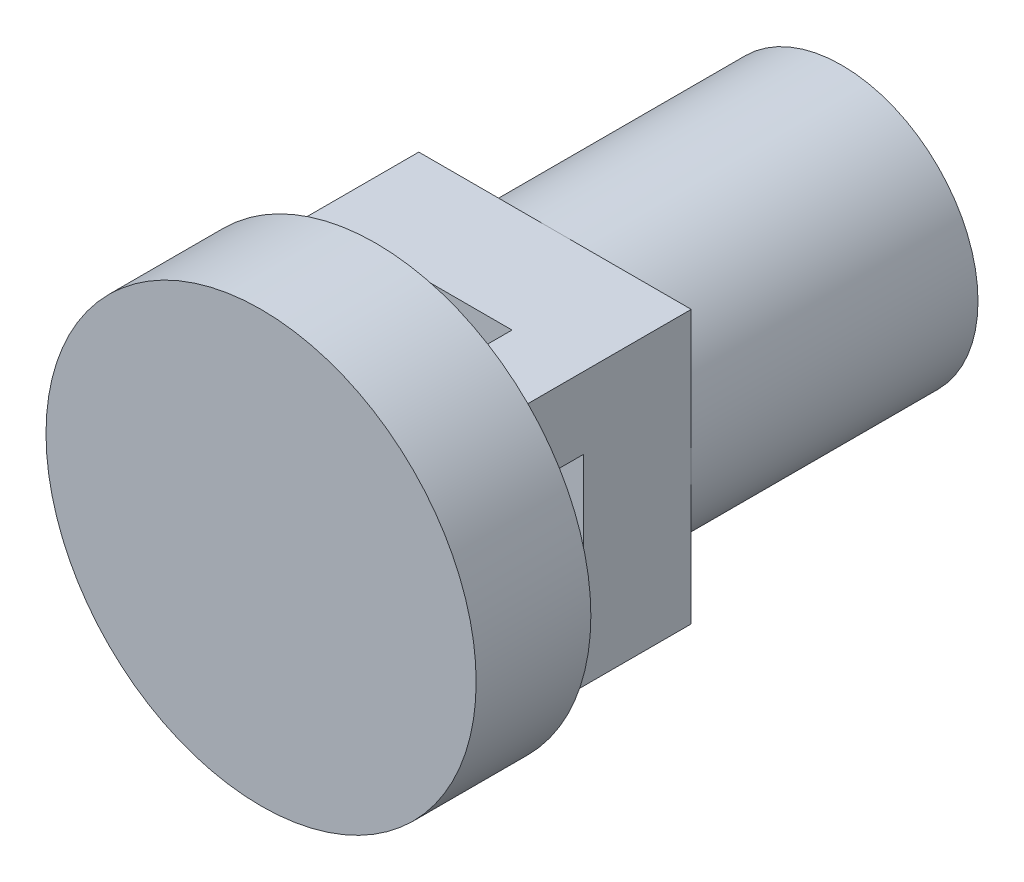
SolidWorks part; units mm, degrees
ref_plane "前视基准面" through (0, 0, 0) normal (0, 0, 1) x (1, 0, 0)
ref_plane "上视基准面" through (0, 0, 0) normal (0, 1, 0) x (1, 0, 0)
ref_plane "右视基准面" through (0, 0, 0) normal (1, 0, 0) x (0, 0, -1)
sketch "草图2" plane through (0, 0, 0) normal (0, 0, 1) x (1, 0, 0)
sketch_block_instance "DXF_ScannerMount_2023-05-06-1"
sketch_block "块1"
sketch "草图3" plane through (0, 0, 0) normal (0, 0, 1) x (1, 0, 0)
  circle A0 centre (3, 3) radius 3
extrude "凸台-拉伸1" add sketch "草图3" along normal blind 1.6
sketch "草图4" plane through (0, 0, 0) normal (0, 0, -1) x (-1, 0, 0)
  line L1 (-1.1, 1.1) -> (-2.1, 1.1)
  line L2 (-1.1, 1.1) -> (-1.1, 2.1)
  line L3 (-1.1, 2.1) -> (-2.1, 2.1)
  line L4 (-2.1, 1.1) -> (-2.1, 2.1)
  line L5 (-1.1, 3.9001) -> (-2.1, 3.9001)
  line L6 (-1.1, 3.9001) -> (-1.1, 4.9001)
  line L7 (-1.1, 4.9001) -> (-2.1, 4.9001)
  line L8 (-2.1, 3.9001) -> (-2.1, 4.9001)
  line L9 (-3.9001, 3.9001) -> (-4.9001, 3.9001)
  line L10 (-3.9001, 3.9001) -> (-3.9001, 4.9001)
  line L11 (-3.9001, 4.9001) -> (-4.9001, 4.9001)
  line L12 (-4.9001, 3.9001) -> (-4.9001, 4.9001)
  line L13 (-3.9001, 1.1) -> (-4.9001, 1.1)
  line L14 (-3.9001, 1.1) -> (-3.9001, 2.1)
  line L15 (-3.9001, 2.1) -> (-4.9001, 2.1)
  line L16 (-4.9001, 1.1) -> (-4.9001, 2.1)
extrude "凸台-拉伸2" add sketch "草图4" along normal blind 1
sketch "草图5" plane through (0, 0, -1) normal (0, 0, -1) x (-1, 0, 0)
  line L1 (-1.1, 1.1) -> (-4.9001, 1.1)
  line L2 (-1.1, 1.1) -> (-1.1, 4.9001)
  line L3 (-1.1, 4.9001) -> (-4.9001, 4.9001)
  line L4 (-4.9001, 1.1) -> (-4.9001, 4.9001)
extrude "凸台-拉伸3" add sketch "草图5" along normal blind 1.5
sketch "草图6" plane through (0, 0, -2.5) normal (0, 0, -1) x (-1, 0, 0)
  circle A0 centre (-3, 3) radius 1.9001
extrude "凸台-拉伸4" add sketch "草图6" along normal blind 4
sketch "草图7" plane through (0, 0, -6.5) normal (0, 0, -1) x (-1, 0, 0)
  circle A0 centre (-3, 3) radius 1.6152
extrude "切除-拉伸1" cut sketch "草图7" against normal blind 4
sketch "草图8" plane through (0, 0, -2.5) normal (0, 0, -1) x (-1, 0, 0)
  circle A0 centre (-3, 3) radius 0.6016
extrude "凸台-拉伸5" add sketch "草图8" along normal blind 3
sketch "草图9" plane through (0, 0, -5.5) normal (0, 0, -1) x (-1, 0, 0)
  circle A0 centre (-3, 3) radius 0.3066
extrude "切除-拉伸2" cut sketch "草图9" against normal blind 3
sketch "草图10" plane through (0, 0, -5.5) normal (0, 0, -1) x (-1, 0, 0)
  line L1 (-2.8847, 2.1684) -> (-3.1134, 2.1684)
  line L2 (-2.8847, 2.1684) -> (-2.8847, 3.8241)
  line L3 (-2.8847, 3.8241) -> (-3.1134, 3.8241)
  line L4 (-3.1134, 2.1684) -> (-3.1134, 3.8241)
extrude "切除-拉伸3" cut sketch "草图10" against normal blind 3
